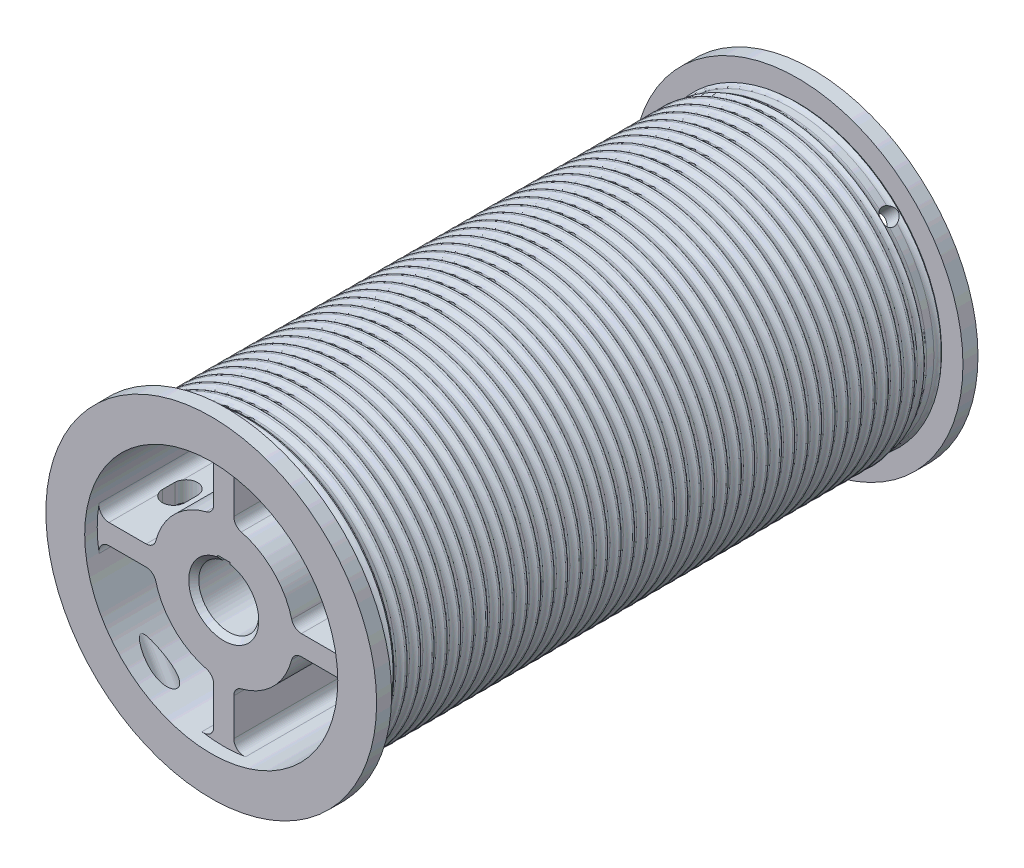
SolidWorks part; units mm, degrees
ref_plane "Front" through (0, 0, 0) normal (0, 0, 1) x (1, 0, 0)
ref_plane "Top" through (0, 0, 0) normal (0, 1, 0) x (1, 0, 0)
ref_plane "Right" through (0, 0, 0) normal (1, 0, 0) x (0, 0, -1)
ref_plane "Plane1" through (0, 0, 0) normal (0, 0, 1) x (1, 0, 0)
ref_plane "Plane2" through (0, 0, 0) normal (0, 1, 0) x (-1, 0, 0)
ref_plane "Plane3" through (0, 0, 0) normal (1, 0, 0) x (0, 0, -1)
sketch "Sketch1" plane through (0, 0, 0) normal (0, 0, 1) x (1, 0, 0)
  line L0 (6.35, -49.1869) -> (6.35, -72.7181)
  line L1 (-6.35, -49.1869) -> (-6.35, -72.7181)
  line L2 (-49.1869, -6.35) -> (-72.7181, -6.35)
  line L3 (-49.1869, 6.35) -> (-72.7181, 6.35)
  line L4 (6.35, 49.1869) -> (6.35, 72.7181)
  line L5 (-6.35, 49.1869) -> (-6.35, 72.7181)
  line L6 (49.1869, 6.35) -> (72.7181, 6.35)
  line L7 (49.1869, -6.35) -> (72.7181, -6.35)
  arc A0 (-78.9734, -13.7925) -> (-13.7925, -78.9734) centre (0, 0) ccw
  arc A1 (13.7925, -78.9734) -> (78.9734, -13.7925) centre (0, 0) ccw
  arc A2 (-43.0385, -11.1125) -> (-11.1125, -43.0385) centre (0, 0) ccw
  arc A3 (11.1125, -43.0385) -> (43.0385, -11.1125) centre (0, 0) ccw
  circle A4 centre (0, 0) radius 90.678
  arc A5 (6.35, -72.7181) -> (13.7925, -78.9734) centre (12.7, -72.7181) ccw
  arc A6 (-13.7925, -78.9734) -> (-6.35, -72.7181) centre (-12.7, -72.7181) ccw
  arc A7 (-6.35, -49.1869) -> (-11.1125, -43.0385) centre (-12.7, -49.1869) ccw
  arc A8 (11.1125, -43.0385) -> (6.35, -49.1869) centre (12.7, -49.1869) ccw
  arc A9 (-13.7925, 78.9734) -> (-78.9734, 13.7925) centre (0, 0) ccw
  arc A10 (43.0385, 11.1125) -> (11.1125, 43.0385) centre (0, 0) ccw
  arc A11 (13.7925, 78.9734) -> (6.35, 72.7181) centre (12.7, 72.7181) ccw
  arc A12 (-11.1125, 43.0385) -> (-43.0385, 11.1125) centre (0, 0) ccw
  arc A13 (-49.1869, 6.35) -> (-43.0385, 11.1125) centre (-49.1869, 12.7) ccw
  arc A14 (-78.9734, 13.7925) -> (-72.7181, 6.35) centre (-72.7181, 12.7) ccw
  arc A15 (-72.7181, -6.35) -> (-78.9734, -13.7925) centre (-72.7181, -12.7) ccw
  arc A16 (-43.0385, -11.1125) -> (-49.1869, -6.35) centre (-49.1869, -12.7) ccw
  circle A17 centre (0, 0) radius 12.7
  arc A18 (-6.35, 72.7181) -> (-13.7925, 78.9734) centre (-12.7, 72.7181) ccw
  arc A19 (-11.1125, 43.0385) -> (-6.35, 49.1869) centre (-12.7, 49.1869) ccw
  arc A20 (6.35, 49.1869) -> (11.1125, 43.0385) centre (12.7, 49.1869) ccw
  arc A21 (78.9734, 13.7925) -> (13.7925, 78.9734) centre (0, 0) ccw
  arc A22 (43.0385, 11.1125) -> (49.1869, 6.35) centre (49.1869, 12.7) ccw
  arc A23 (49.1869, -6.35) -> (43.0385, -11.1125) centre (49.1869, -12.7) ccw
  arc A24 (72.7181, 6.35) -> (78.9734, 13.7925) centre (72.7181, 12.7) ccw
  arc A25 (78.9734, -13.7925) -> (72.7181, -6.35) centre (72.7181, -12.7) ccw
ref_plane "END PLANE" through (0, 0, -381) normal (0, 0, 1) x (1, 0, 0)
extrude "Extrude1" add sketch "Sketch1" against normal up to surface (381 mm away) up to plane "END PLANE"
sketch "Sketch2" plane through (0, 0, 0) normal (0, 0, 1) x (1, 0, 0)
  circle A0 centre (0, 0) radius 104.775
  circle A1 centre (0, 0) radius 90.678
  dimension "D1" = 209.55
  dimension "D2" = 181.356
extrude "Extrude2" add sketch "Sketch2" against normal blind 9.525
sketch "Sketch3" plane through (0, 0, -381) normal (0, 0, 1) x (1, 0, 0)
  circle A0 centre (0, 0) radius 104.775
  circle A1 centre (0, 0) radius 90.678
  dimension "D1" = 209.55
  dimension "D2" = 181.356
extrude "Extrude4" add sketch "Sketch3" along normal blind 9.525
sketch "Sketch4" plane through (0, 0, 0) normal (0, 0, 1) x (1, 0, 0)
  line L0 (3.9688, 22.8067) -> (-3.9688, 22.8067)
  line L1 (3.9688, 18.584) -> (3.9688, 22.8067)
  line L2 (-3.9688, 18.584) -> (-3.9688, 22.8067)
  arc A0 (-3.9688, 18.584) -> (3.9688, 18.584) centre (0, 0) ccw
extrude "Cut-Extrude1" cut sketch "Sketch4" against normal blind 63.5
sketch "Sketch5" plane through (0, 0, 0) normal (0, 0, 1) x (1, 0, 0)
  circle A0 centre (0, 0) radius 80.1688
  dimension "D1" = 160.3375
extrude "Cut-Extrude2" cut sketch "Sketch5" against normal blind 7.9375
sketch "Sketch6" plane through (0, 0, -381) normal (0, 0, 1) x (1, 0, 0)
  circle A0 centre (0, 0) radius 80.1688
  dimension "D1" = 160.3375
extrude "Cut-Extrude3" cut sketch "Sketch6" along normal blind 7.9375
sketch "Sketch8" plane through (0, 0, 0) normal (1, 0, 0) x (0, 0, -1)
  line L0 (17.9832, 90.678) -> (9.525, 90.678)
  line L1 (50, 0) -> (-50, 0) construction
  line L2 (0, 50) -> (0, -50) construction
  arc A0 (14.384, 92.8548) -> (17.9832, 90.678) centre (17.9832, 94.742) ccw
  arc A1 (9.525, 90.678) -> (13.1242, 92.8548) centre (9.525, 94.742) ccw
  arc A2 (14.384, 92.8548) -> (13.1242, 92.8548) centre (13.7541, 92.5245) ccw
  dimension "D1" = 0.7112
  dimension "D2" = 4.064
  dimension "D3" = 4.064
  dimension "D4" = 8.4582
  dimension "D5" = 90.678
  dimension "D6" = 9.525
revolve "Revolve1" add sketch "Sketch8" angle 360 about axis through (0, 0, -9.525) along (0, 0, 1)
pattern_linear "LPattern1" count 43 spacing 8.4667 along (0, 0, -1) of "Revolve1"
sketch "Sketch9" plane through (0, 0, 0) normal (1, 0, 0) x (0, 0, -1)
  line L1 (13.589, 90.424) -> (18.161, 90.424)
  line L2 (9.525, 94.488) -> (9.525, 95.1865)
  line L3 (9.525, 95.1865) -> (22.225, 95.1865)
  line L4 (22.225, 94.488) -> (22.225, 95.1865)
  line L5 (0, 50) -> (0, -50) construction
  line L6 (50, 0) -> (-50, 0) construction
  arc A0 (13.589, 90.424) -> (9.525, 94.488) centre (13.589, 94.488) cw
  arc A1 (22.225, 94.488) -> (18.161, 90.424) centre (18.161, 94.488) cw
  dimension "D2" = 4.064
  dimension "D4" = 4.7625
  dimension "D5" = 4.572
  dimension "D1" = 9.525
  dimension "D3" = 90.424
revolve "Cut-Revolve1" cut sketch "Sketch9" angle 360 about axis through (0, 0, -9.525) along (0, 0, 1)
sketch "Sketch11" plane through (0, 0, 0) normal (1, 0, 0) x (0, 0, -1)
  line L1 (367.411, 90.424) -> (362.839, 90.424)
  line L2 (371.475, 94.488) -> (371.475, 95.1865)
  line L3 (371.475, 95.1865) -> (358.775, 95.1865)
  line L4 (358.775, 94.488) -> (358.775, 95.1865)
  line L6 (381, 50) -> (381, -50) construction
  line L7 (50, 0) -> (-50, 0) construction
  arc A0 (358.775, 94.488) -> (362.839, 90.424) centre (362.839, 94.488) ccw
  arc A1 (371.475, 94.488) -> (367.411, 90.424) centre (367.411, 94.488) cw
  dimension "D5" = 4.064
  dimension "D1" = 12.7
  dimension "D2" = 4.7625
  dimension "D3" = 9.525
  dimension "D4" = 90.424
revolve "Cut-Revolve2" cut sketch "Sketch11" angle 360 about axis through (0, 0, -9.525) along (0, 0, 1)
ref_plane "Plane5" through (0, 0, 0) normal (-0.4924, 0.8704, 0) x (-0.8704, -0.4924, 0)
sketch "Sketch12" plane through (0, 0, 0) normal (-0.4924, 0.8704, 0) x (-0.8704, -0.4924, 0)
  line L0 (50, 0) -> (-50, 0) construction
  line L1 (0, -373.0625) -> (0, -7.9375) construction
  circle A0 centre (73.025, -15.875) radius 5.5563
  dimension "D1" = 11.1125
  dimension "D2" = 15.875
  dimension "D3" = 73.025
extrude "Cut-Extrude5" cut sketch "Sketch12" against normal through all
ref_plane "Plane6" through (0, 0, 0) normal (0.7071, 0.7071, 0) x (-0.7071, 0.7071, 0)
hole_wizard "3/8-16 Tapped Hole1" positions "Sketch14" profile "Sketch13" tap size "3/8-16" standard "Ansi Inch"
sketch "Sketch14" plane through (0, 0, 0) normal (0.7071, 0.7071, 0) x (-0.7071, 0.7071, 0)
  line L1 (0, -9.525) -> (0, 0) construction
  line L2 (50, -381) -> (-50, -381) construction
  point P0 (0, -365.125)
  dimension "D1" = 15.875
sketch "Sketch13" plane through (0, 0, -365.125) normal (0, 0, 1) x (0.7071, -0.7071, 0)
  line L0 (0, 0) -> (0, 100.8097)
  line L1 (0, 100.8097) -> (3.9687, 98.425)
  line L2 (3.9687, 98.425) -> (3.9687, 0)
  line L5 (3.9687, 0) -> (0, 0)
  line L10 (0, 100.8097) -> (-3.9688, 98.425) construction
  line L11 (0, -6.35) -> (0, 107.95) construction
  dimension "Tap Drill Dia." = 7.9375
  dimension "Tap Drill Depth" = 98.425
  dimension "Drill Angle" = 118
ref_plane "Plane7" through (71.842, 71.842, 0) normal (0.7071, 0.7071, 0) x (0, 0, -1)
sketch "Sketch18" plane through (71.842, 71.842, 0) normal (0.7071, 0.7071, 0) x (0, 0, -1)
  line L0 (381, -104.775) -> (381, 104.775) construction
  line L1 (373.0625, 0) -> (7.9375, 0) construction
  circle A0 centre (365.125, 0) radius 5.1594
  dimension "D1" = 10.3187
  dimension "D2" = 15.875
extrude "Cut-Extrude6" cut sketch "Sketch18" against normal blind 25.4
sketch "Sketch19" plane through (0, 0, 0) normal (0, 1, 0) x (-1, 0, 0)
  line L4 (0, 50) -> (0, -50) construction
  line L5 (-59.5312, -330.2) -> (-59.5312, -338.1375)
  line L6 (-73.8188, -330.2) -> (-73.8187, -338.1375)
  line L7 (104.775, 0) -> (-104.775, 0) construction
  line L12 (50, -381) -> (-50, -381) construction
  line L14 (-59.5313, -42.8625) -> (-59.5313, -50.8)
  line L15 (-73.8187, -42.8625) -> (-73.8187, -50.8)
  arc A0 (-59.5312, -330.2) -> (-73.8188, -330.2) centre (-66.675, -330.2) ccw
  arc A1 (-73.8187, -338.1375) -> (-59.5312, -338.1375) centre (-66.675, -338.1375) ccw
  arc A2 (-59.5313, -42.8625) -> (-73.8187, -42.8625) centre (-66.675, -42.8625) ccw
  arc A3 (-73.8187, -50.8) -> (-59.5313, -50.8) centre (-66.675, -50.8) ccw
  dimension "D2" = 7.1438
  dimension "D3" = 14.2875
  dimension "D7" = 14.2875
  dimension "D8" = 7.1438
  dimension "D9" = 7.1438
  dimension "D4" = 7.9375
  dimension "D5" = 42.8625
  dimension "D6" = 66.675
  dimension "D10" = 7.9375
  dimension "D11" = 42.8625
  dimension "D12" = 66.675
extrude "Cut-Extrude7" cut sketch "Sketch19" along normal up to next and the other way up to next
mirror "Mirror1" about plane through (0, 0, 0) normal (1, 0, 0) of "Cut-Extrude7"
sketch "Sketch20" plane through (0, 0, 0) normal (1, 0, 0) x (0, 0, -1)
  line L0 (66.675, 0) -> (66.675, 34.925)
  line L1 (50, 0) -> (-50, 0) construction
  line L2 (314.325, 0) -> (314.325, 34.925)
  line L3 (381, -80.1688) -> (381, 80.1688) construction
  line L4 (142.6222, 64.1355) -> (66.675, 34.925)
  line L5 (238.3778, 64.1355) -> (314.325, 34.925)
  line L6 (314.325, 0) -> (66.675, 0)
  line L7 (0, 50) -> (0, -50) construction
  line L8 (381, 50) -> (381, -50) construction
  line L9 (156.2993, 66.675) -> (224.7007, 66.675)
  arc A0 (156.2993, 66.675) -> (142.6222, 64.1355) centre (156.2993, 28.575) ccw
  arc A1 (238.3778, 64.1355) -> (224.7007, 66.675) centre (224.7007, 28.575) ccw
  point P16 (149.225, 66.675)
  point P19 (231.775, 66.675)
  dimension "D7" = 66.675
  dimension "D8" = 38.1
  dimension "D1" = 66.675
  dimension "D2" = 66.675
  dimension "D3" = 149.225
  dimension "D4" = 149.225
  dimension "D5" = 34.925
  dimension "D6" = 34.925
revolve "Cut-Revolve3" cut sketch "Sketch20" angle 360 about axis through (0, 0, -637.4761) along (0, 0, 1)
sketch "Sketch21" plane through (0, 0, -373.0625) normal (0, 0, -1) x (-1, 0, 0)
  circle A0 centre (0, 0) radius 17.4816
  dimension "D1" = 34.9631
extrude "Cut-Extrude8" cut sketch "Sketch21" against normal blind 85.725
chamfer "Chamfer1" distance 3.175 angle 45 2 edges at (-17.4816, 0, -373.0625) (0, -19.003, -7.9375)
